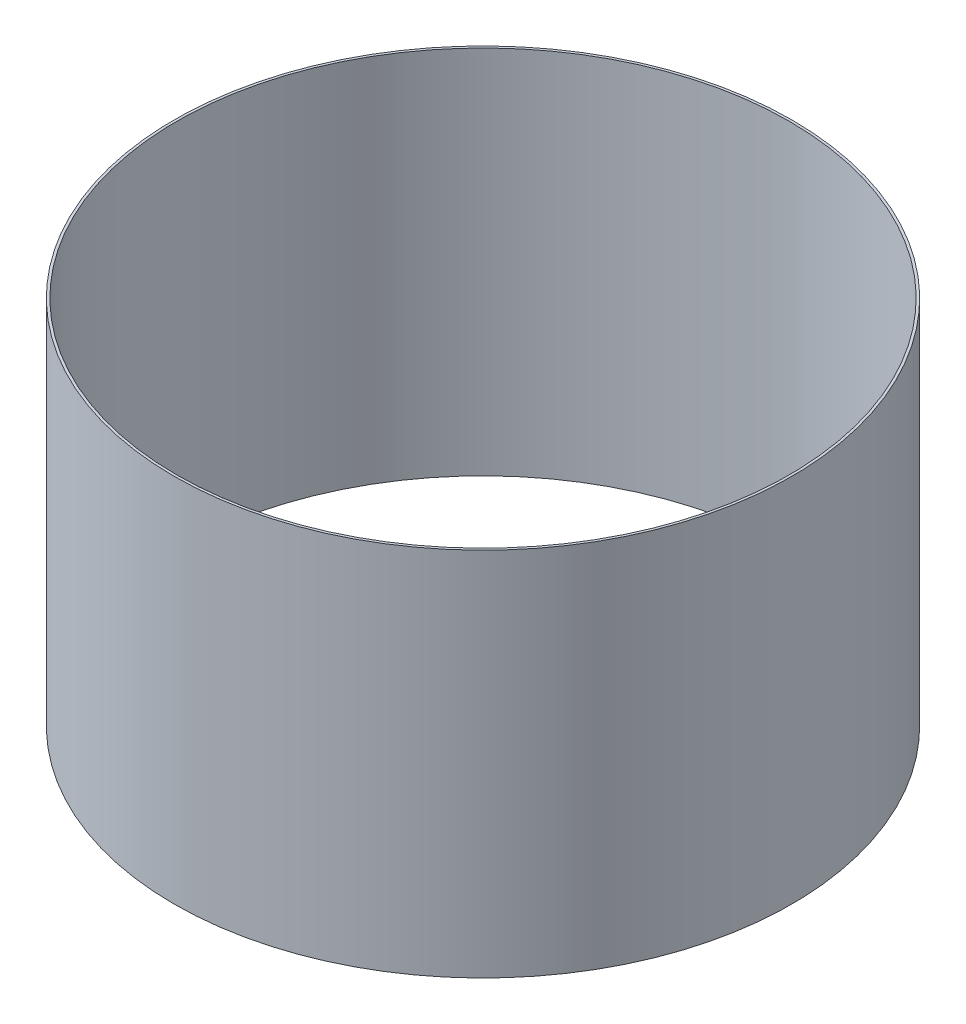
SolidWorks part; units mm, degrees
ref_plane "Front Plane" through (0, 0, 0) normal (0, 0, 1) x (1, 0, 0)
ref_plane "Top Plane" through (0, 0, 0) normal (0, 1, 0) x (1, 0, 0)
ref_plane "Right Plane" through (0, 0, 0) normal (1, 0, 0) x (0, 0, -1)
sketch "Sketch1" plane through (0, 0, 0) normal (0, 0, 1) x (1, 0, 0)
  line L0 (0, 0) -> (0, -260183.0175) construction
  line L1 (-248, 300) -> (-248, 0)
  line L2 (-248, 0) -> (-250, 0)
  line L4 (-248, 300) -> (-250, 300)
  line L5 (-250, 0) -> (-250, 300)
  dimension "D1" = 500
  dimension "D2" = 300
  dimension "D3" = 2
revolve "Revolve1" add sketch "Sketch1" angle 360 about L0
